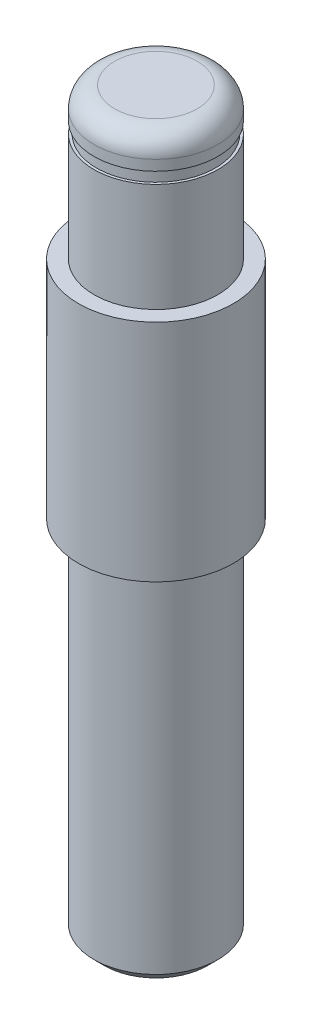
SolidWorks part; units mm, degrees
ref_plane "Front Plane" through (0, 0, 0) normal (0, 0, 1) x (1, 0, 0)
ref_plane "Top Plane" through (0, 0, 0) normal (0, 1, 0) x (1, 0, 0)
ref_plane "Right Plane" through (0, 0, 0) normal (1, 0, 0) x (0, 0, -1)
sketch "Sketch1" plane through (0, 0, 0) normal (0, 0, 1) x (1, 0, 0)
  line L0 (0, 71.4) -> (0, 0)
  line L1 (0, 0) -> (5, 0)
  line L2 (6, 1) -> (6, 35)
  line L3 (6, 35) -> (7.5, 35)
  line L4 (7.5, 35) -> (7.5, 56.8)
  line L5 (7.5, 56.8) -> (6, 56.8)
  line L6 (6, 56.8) -> (6, 67.3)
  line L7 (6, 67.3) -> (5.75, 67.3)
  line L8 (5.75, 67.3) -> (5.75, 68.4)
  line L9 (5.75, 68.4) -> (6, 68.4)
  line L10 (6, 68.4) -> (6, 69.4)
  line L11 (4, 71.4) -> (0, 71.4)
  line L12 (5, 0) -> (6, 1)
  arc A0 (4, 71.4) -> (6, 69.4) centre (4, 69.4) cw
  point P0 (5.875, 67.3)
  point P4 (6, 0)
  dimension "D9" = 2
  dimension "D1" = 7.5
  dimension "D2" = 6
  dimension "D3" = 35
  dimension "D4" = 3
  dimension "D5" = 1.1
  dimension "D6" = 0.25
  dimension "D7" = 10.5
  dimension "D8" = 21.8
revolve "Revolve1" add sketch "Sketch1" angle 360 about L0
